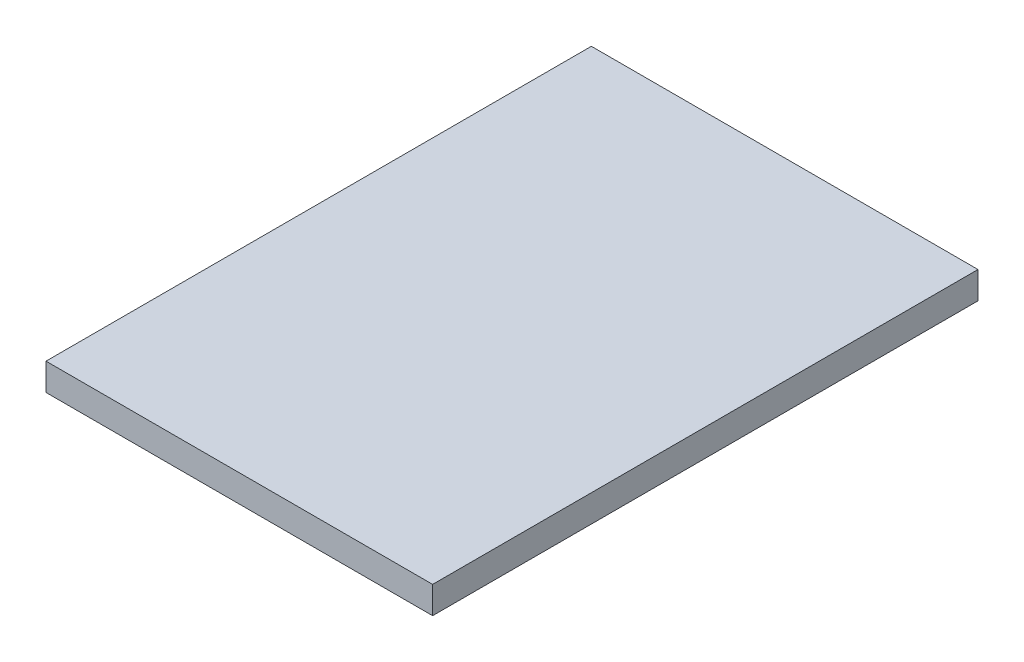
SolidWorks part; units mm, degrees
ref_plane "Front Plane" through (0, 0, 0) normal (0, 0, 1) x (1, 0, 0)
ref_plane "Top Plane" through (0, 0, 0) normal (0, 1, 0) x (1, 0, 0)
ref_plane "Right Plane" through (0, 0, 0) normal (1, 0, 0) x (0, 0, -1)
sketch "Sketch1" plane through (0, 0, 0) normal (0, 1, 0) x (1, 0, 0)
  line L1 (0, 0) -> (42.72, 0)
  line L2 (0, 0) -> (0, 60.26)
  line L3 (0, 60.26) -> (42.72, 60.26)
  line L4 (42.72, 0) -> (42.72, 60.26)
  line L5 (0, 0) -> (42.72, 60.26) construction
  line L6 (0, 60.26) -> (42.72, 0) construction
  point P4 (21.36, 30.13)
  dimension "D1" = 42.72
  dimension "D2" = 60.26
extrude "Boss-Extrude1" add sketch "Sketch1" along normal blind 3
